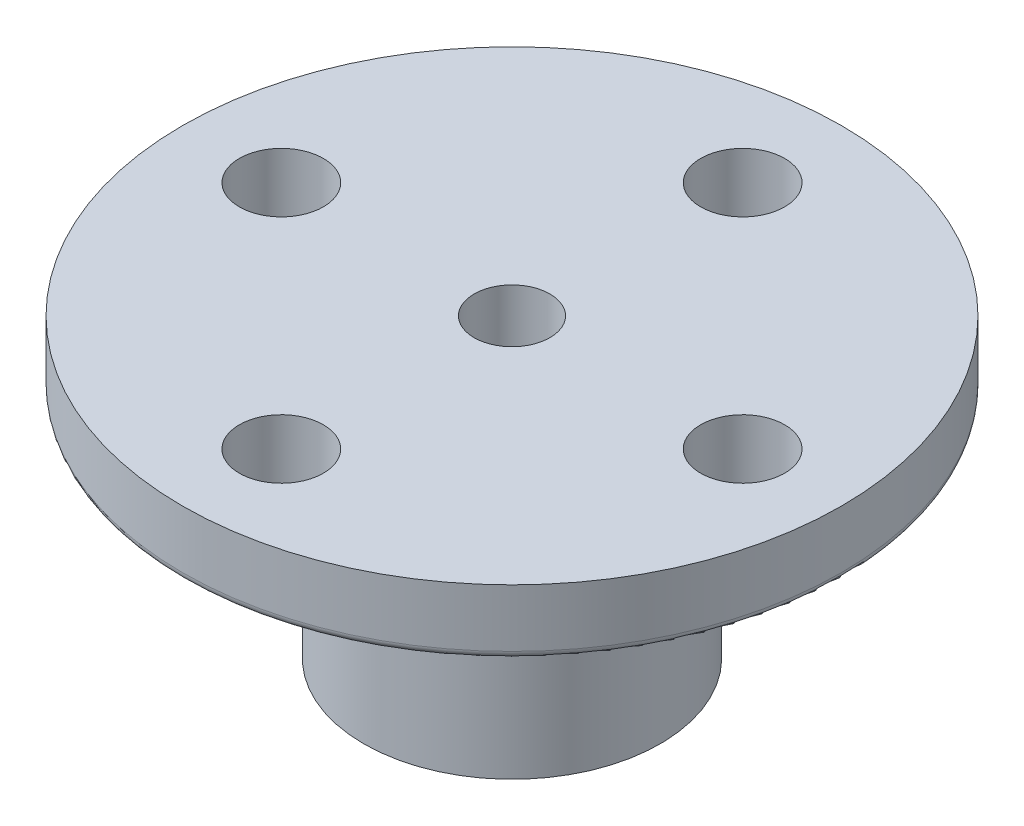
SolidWorks part; units mm, degrees
material "ABS"
ref_plane "Front Plane" through (0, 0, 0) normal (0, 0, 1) x (1, 0, 0)
ref_plane "Top Plane" through (0, 0, 0) normal (0, 1, 0) x (1, 0, 0)
ref_plane "Right Plane" through (0, 0, 0) normal (1, 0, 0) x (0, 0, -1)
sketch "Sketch1" plane through (0, 0, 0) normal (0, 1, 0) x (1, 0, 0)
  circle A0 centre (0, 0) radius 10
  dimension "D1" = 20
extrude "Boss-Extrude1" add sketch "Sketch1" along normal blind 2
sketch "Sketch2" plane through (0, 0, 0) normal (0, 1, 0) x (1, 0, 0)
  circle A0 centre (0, 0) radius 4.5
  dimension "D1" = 9
extrude "Boss-Extrude2" add sketch "Sketch2" against normal blind 7
sketch "Sketch3" plane through (0, 0, 0) normal (0, 1, 0) x (1, 0, 0)
  line L0 (0, 16.6668) -> (0, -17.2828) construction
  line L1 (-21.9372, 0) -> (30.2192, 0) construction
  line L2 (-7, 16.6668) -> (-7, -16.6668) construction
  line L3 (-15.9139, 7) -> (17.4197, 7) construction
  circle A0 centre (0, 7) radius 1.275
  circle A1 centre (-7, 0) radius 1.275
  circle A2 centre (0, -7) radius 1.275
  circle A3 centre (7, 0) radius 1.275
  dimension "D3" = 2.55
  dimension "D4" = 2.55
  dimension "D1" = 7
  dimension "D2" = 7
extrude "Cut-Extrude1" cut sketch "Sketch3" along normal through all
cosmetic thread "Cosmetic Thread1" parameters "D2"=2.87
cosmetic thread "Cosmetic Thread2" parameters "D2"=2.87
cosmetic thread "Cosmetic Thread3" parameters "D2"=2.87
cosmetic thread "Cosmetic Thread4" parameters "D2"=2.87
fillet "Fillet1" radius 0.25 1 edges at (0, 0, 10)
sketch "Sketch6" plane through (0, 2, 0) normal (0, 1, 0) x (1, 0, 0)
  circle A0 centre (0, 0) radius 1.15
  dimension "D1" = 2.3
extrude "Cut-Extrude2" cut sketch "Sketch6" against normal through all
sketch "Sketch7" plane through (0, -7, 0) normal (0, -1, 0) x (1, 0, 0)
  circle A0 centre (0, 0) radius 3.25
  dimension "D1" = 6.5
extrude "Cut-Extrude3" cut sketch "Sketch7" against normal blind 2.5
sketch3d "3DSketch1"
  line L0 (0, 0, 0) -> (0, -47.4119, 0) construction
sketch "Sketch8" plane through (0, -7, 0) normal (0, -1, 0) x (1, 0, 0)
  line L1 (-2.6782, -1.107) -> (-3.0738, -1.003)
  line L2 (-2.6782, -1.107) -> (-2.8493, -1.4785)
  arc A1 (-3.0738, -1.003) -> (-2.8493, -1.4785) centre (-0.3499, -0.0079) ccw
  circle A4 centre (0, 0) radius 3.25 construction
  dimension "D4" = 0.409
  dimension "D3" = 5.8
  dimension "D1" = 80
  dimension "D2" = 0.5258
extrude "Boss-Extrude4" add sketch "Sketch8" against normal blind 2.5
pattern_circular "CirPattern1" count 26 over 360 about axis through (0, 0, 0) along (0, 1, 0) of "Boss-Extrude4"
